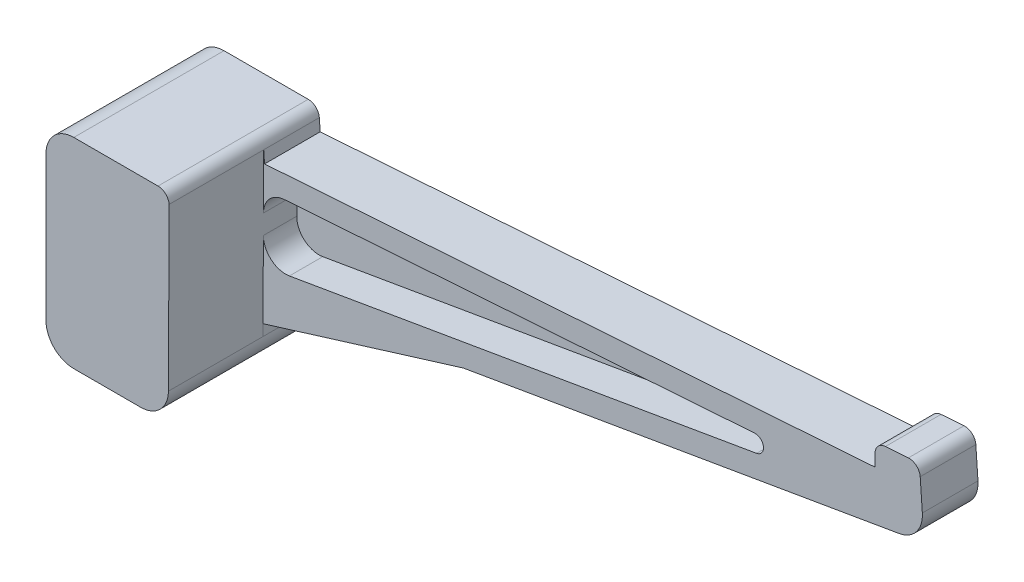
SolidWorks part; units mm, degrees
ref_plane "Front Plane" through (0, 0, 0) normal (0, 0, 1) x (1, 0, 0)
ref_plane "Top Plane" through (0, 0, 0) normal (0, 1, 0) x (1, 0, 0)
ref_plane "Right Plane" through (0, 0, 0) normal (1, 0, 0) x (0, 0, -1)
sketch "Sketch1" plane through (0, 0, 0) normal (0, 0, 1) x (1, 0, 0)
  line L0 (-5, 10) -> (10.135, 10)
  line L1 (12.1301, 8.1395) -> (12.279, 6.0097)
  line L2 (12.279, 6.0097) -> (122.0111, 13.683)
  line L3 (122.0111, 13.683) -> (122.0111, 15.8277)
  line L4 (123.8716, 17.8228) -> (127.9965, 18.1113)
  line L5 (130.1311, 16.2556) -> (130.513, 10.7938)
  line L6 (12, -21) -> (12, -14.0586)
  line L7 (7, -26) -> (-5, -26)
  line L8 (-10, -21) -> (-10, -14)
  line L9 (12, -14.0586) -> (126.3687, 5.5166)
  line L10 (-10, -2) -> (-3, -2)
  line L11 (-3, -2) -> (-3, 2)
  line L12 (-1, 4) -> (4, 4)
  line L13 (6, 2) -> (6, -18)
  line L14 (4, -20) -> (-1, -20)
  line L15 (-3, -18) -> (-3, -14)
  line L16 (-3, -14) -> (-10, -14)
  line L17 (-10, -2) -> (-10, 5)
  arc A0 (-1, -20) -> (-3, -18) centre (-1, -18) cw
  arc A1 (6, -18) -> (4, -20) centre (4, -18) cw
  arc A2 (130.513, 10.7938) -> (126.3687, 5.5166) centre (125.5252, 10.445) cw
  arc A3 (12, -21) -> (7, -26) centre (7, -21) cw
  arc A4 (-5, -26) -> (-10, -21) centre (-5, -21) cw
  arc A5 (-5, 10) -> (-10, 5) centre (-5, 5) ccw
  arc A6 (127.9965, 18.1113) -> (130.1311, 16.2556) centre (128.136, 16.1161) cw
  arc A7 (122.0111, 15.8277) -> (123.8716, 17.8228) centre (124.0111, 15.8277) cw
  arc A8 (10.135, 10) -> (12.1301, 8.1395) centre (10.135, 8) cw
  arc A9 (4, 4) -> (6, 2) centre (4, 2) cw
  arc A10 (-3, 2) -> (-1, 4) centre (-1, 2) cw
  point P17 (130.8287, 6.28)
  point P20 (12, -26)
  point P25 (-10, 10)
  point P28 (129.9916, 18.2508)
  point P31 (122.0111, 17.6927)
  point P34 (12, 10)
  point P40 (-3, -20)
  point P44 (6, -20)
  dimension "D2" = 10
  dimension "D13" = 5
  dimension "D14" = 2
  dimension "D19" = 2
  dimension "D3" = 26
  dimension "D4" = 6
  dimension "D5" = 6
  dimension "D6" = 7
  dimension "D7" = 4
  dimension "D8" = 110
  dimension "D9" = 4
  dimension "D10" = 8
  dimension "D11" = 12
  dimension "D12" = 20
  dimension "D15" = 10
  dimension "D16" = 12
  dimension "D17" = 9
  dimension "D18" = 22
extrude "Boss-Extrude1" add sketch "Sketch1" along normal blind 10
sketch "Sketch4" plane through (0, 0, 10) normal (0, 0, 1) x (1, 0, 0)
  line L0 (12, -18.9903) -> (48, -7.8969)
  line L1 (12, -21) -> (12, -14.0586) construction
  line L2 (12, -14.0586) -> (126.3687, 5.5166) construction
  line L3 (48, -7.8969) -> (12, -14.0586)
  line L4 (12, -14.0586) -> (12, -18.9903)
  dimension "D1" = 25
  dimension "D2" = 36
extrude "Boss-Extrude2" add sketch "Sketch4" against normal up to surface (10 mm away) up to face at (31.1995, -2.3287, 0)
sketch "Sketch5" plane through (0, 0, 10) normal (0, 0, 1) x (1, 0, 0)
  line L1 (-5, -26) -> (7, -26) construction
  line L2 (-10, -14) -> (-10, -21) construction
  line L3 (-3, -14) -> (-10, -14) construction
  line L4 (-3, -18) -> (-3, -14) construction
  line L5 (4, -20) -> (-1, -20) construction
  line L6 (6, 2) -> (6, -18) construction
  line L7 (-1, 4) -> (4, 4) construction
  line L8 (-3, -2) -> (-3, 2) construction
  line L9 (-10, -2) -> (-3, -2) construction
  line L10 (-10, 5) -> (-10, -2) construction
  line L11 (10.135, 10) -> (-5, 10) construction
  line L12 (12, -21) -> (12.1301, 8.1395)
  line L13 (-5, -26) -> (7, -26)
  line L14 (-10, -14) -> (-10, -21)
  line L15 (-3, -14) -> (-10, -14)
  line L16 (-3, -18) -> (-3, -14)
  line L17 (4, -20) -> (-1, -20)
  line L18 (6, 2) -> (6, -18)
  line L19 (-1, 4) -> (4, 4)
  line L20 (-3, -2) -> (-3, 2)
  line L21 (-10, -2) -> (-3, -2)
  line L22 (-10, 5) -> (-10, -2)
  line L23 (10.135, 10) -> (-5, 10)
  arc A0 (7, -26) -> (12, -21) centre (7, -21) ccw construction
  arc A1 (-10, -21) -> (-5, -26) centre (-5, -21) ccw construction
  arc A2 (-3, -18) -> (-1, -20) centre (-1, -18) ccw construction
  arc A3 (4, -20) -> (6, -18) centre (4, -18) ccw construction
  arc A4 (6, 2) -> (4, 4) centre (4, 2) ccw construction
  arc A5 (-1, 4) -> (-3, 2) centre (-1, 2) ccw construction
  arc A6 (-5, 10) -> (-10, 5) centre (-5, 5) ccw construction
  arc A7 (12.1301, 8.1395) -> (10.135, 10) centre (10.135, 8) ccw construction
  arc A8 (7, -26) -> (12, -21) centre (7, -21) ccw
  arc A9 (-10, -21) -> (-5, -26) centre (-5, -21) ccw
  arc A10 (-3, -18) -> (-1, -20) centre (-1, -18) ccw
  arc A11 (4, -20) -> (6, -18) centre (4, -18) ccw
  arc A12 (6, 2) -> (4, 4) centre (4, 2) ccw
  arc A13 (-1, 4) -> (-3, 2) centre (-1, 2) ccw
  arc A14 (-5, 10) -> (-10, 5) centre (-5, 5) ccw
  arc A15 (12.1301, 8.1395) -> (10.135, 10) centre (10.135, 8) ccw
extrude "Boss-Extrude3" add sketch "Sketch5" along normal blind 15
sketch "Sketch6" plane through (0, 0, 25) normal (0, 0, 1) x (1, 0, 0)
  line L0 (-10, 5) -> (-10, -2) construction
  line L1 (10.135, 10) -> (-5, 10) construction
  line L2 (12, -21) -> (12.1301, 8.1395) construction
  line L3 (-5, -26) -> (7, -26) construction
  line L4 (-10, 5) -> (-10, -21)
  line L5 (10.135, 10) -> (-5, 10)
  line L6 (12, -21) -> (12.1301, 8.1395)
  line L7 (-5, -26) -> (7, -26)
  arc A0 (-5, 10) -> (-10, 5) centre (-5, 5) ccw construction
  arc A1 (12.1301, 8.1395) -> (10.135, 10) centre (10.135, 8) ccw construction
  arc A2 (7, -26) -> (12, -21) centre (7, -21) ccw construction
  arc A3 (-10, -21) -> (-5, -26) centre (-5, -21) ccw construction
  arc A4 (-5, 10) -> (-10, 5) centre (-5, 5) ccw
  arc A5 (12.1301, 8.1395) -> (10.135, 10) centre (10.135, 8) ccw
  arc A6 (7, -26) -> (12, -21) centre (7, -21) ccw
  arc A7 (-10, -21) -> (-5, -26) centre (-5, -21) ccw
extrude "Boss-Extrude4" add sketch "Sketch6" along normal blind 2
sketch "Sketch2" plane through (0, 0, 10) normal (0, 0, 1) x (1, 0, 0)
  line L0 (12.0704, -5.2277) -> (12.0861, -1.7257)
  line L1 (15.807, 2.2467) -> (100.3595, 8.1592)
  line L2 (16.7452, -9.1883) -> (100.7172, 5.1843)
  line L3 (48, -7.8969) -> (126.3687, 5.5166) construction
  line L4 (122.0111, 13.683) -> (12.279, 6.0097) construction
  line L6 (12.009, -18.9875) -> (12.1301, 8.1395) construction
  arc A0 (100.7172, 5.1843) -> (100.3595, 8.1592) centre (100.4641, 6.6628) ccw
  arc A1 (16.7452, -9.1883) -> (12.0704, -5.2277) centre (16.0704, -5.2456) cw
  arc A2 (12.0861, -1.7257) -> (15.807, 2.2467) centre (16.086, -1.7436) cw
  dimension "D1" = 1.5
  dimension "D4" = 4
  dimension "D2" = 4
  dimension "D3" = 4
extrude "Cut-Extrude1" cut sketch "Sketch2" against normal offset from surface (6 mm away) 4 up to face at (31.7595, -2.6787, 0)
